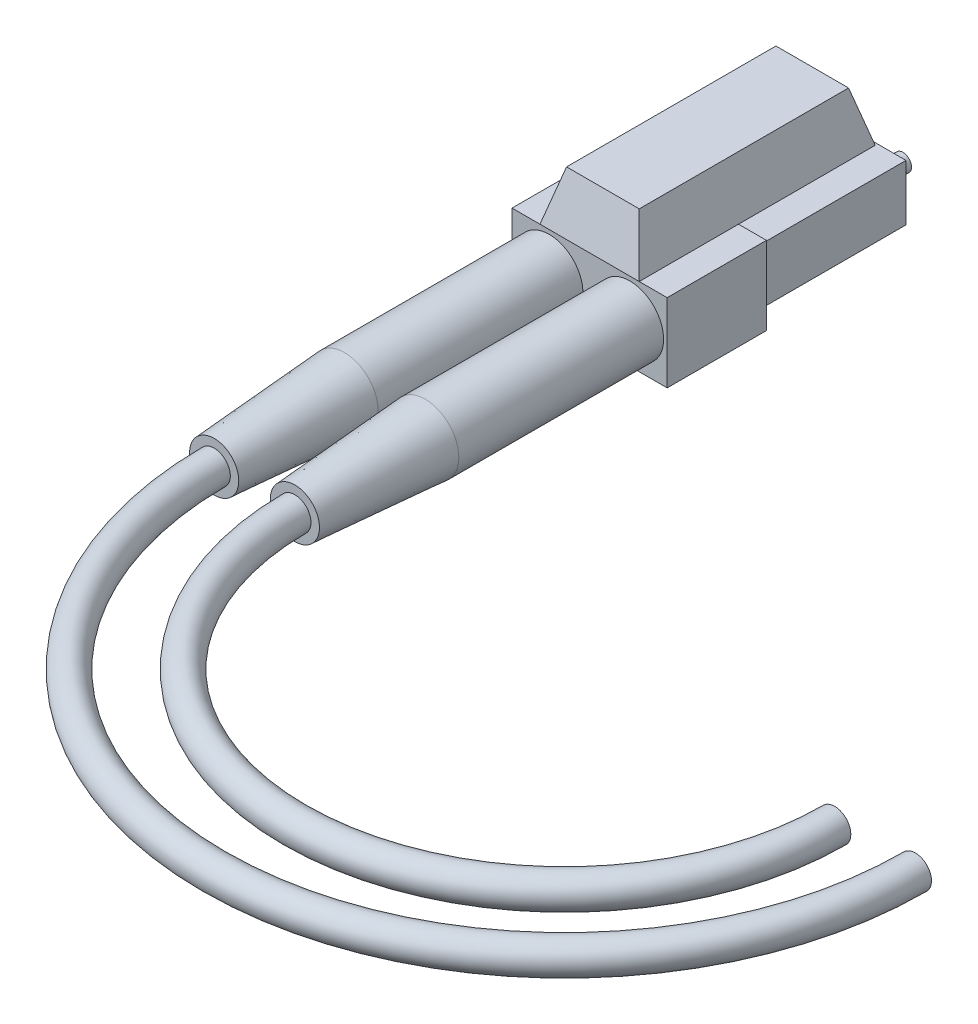
SolidWorks part; units mm, degrees
ref_plane "Front" through (0, 0, 0) normal (0, 0, 1) x (1, 0, 0)
ref_plane "Top" through (0, 0, 0) normal (0, 1, 0) x (1, 0, 0)
ref_plane "Right" through (0, 0, 0) normal (1, 0, 0) x (0, 0, -1)
sketch "Sketch1" plane through (0, 0, 0) normal (0, 0, 1) x (1, 0, 0)
  line L0 (0.9959, 4.5) -> (5.4959, 4.5)
  line L1 (-5.5041, 4.5) -> (-1.0041, 4.5)
  line L2 (-5.5041, 4.5) -> (-5.5041, 0)
  line L3 (-5.5041, 0) -> (-1.0041, 0)
  line L4 (-1.0041, 4.5) -> (-1.0041, 0)
  line L5 (0.9959, 4.5) -> (0.9959, 0)
  line L6 (0.9959, 0) -> (5.4959, 0)
  line L7 (5.4959, 4.5) -> (5.4959, 0)
  dimension "D1" = 2
extrude "Boss-Extrude1" add sketch "Sketch1" against normal blind 12
sketch "Sketch2" plane through (0, 0, -12) normal (0, 0, -1) x (-1, 0, 0)
  circle A0 centre (3.25, 2.25) radius 0.6917
  circle A1 centre (-3.25, 2.25) radius 0.6917
  dimension "D1" = 2
extrude "Boss-Extrude2" add sketch "Sketch2" along normal blind 2
sketch "Sketch3" plane through (0, 0, 0) normal (0, 0, 1) x (1, 0, 0)
  line L1 (-6.25, -1) -> (6.25, -1)
  line L2 (-6.25, -1) -> (-6.25, 5.3)
  line L3 (-6.25, 5.3) -> (6.25, 5.3)
  line L4 (6.25, -1) -> (6.25, 5.3)
extrude "Boss-Extrude3" add sketch "Sketch3" along normal blind 8 contours L1 L4 L3 L2
sketch "Sketch4" plane through (0, 0, 8) normal (0, 0, 1) x (1, 0, 0)
  circle A0 centre (3.25, 2.25) radius 2.715
  circle A1 centre (-3.25, 2.25) radius 2.715
extrude "Boss-Extrude4" add sketch "Sketch4" along normal blind 16.5
sketch "Sketch5" plane through (0, 0, 24.5) normal (0, 0, 1) x (1, 0, 0)
  circle A0 centre (-3.25, 2.25) radius 2.715
  circle A1 centre (3.25, 2.25) radius 2.715
extrude "Boss-Extrude5" add sketch "Sketch5" along normal blind 10.5 draft 4
sketch "Sketch6" plane through (0, 0, 35) normal (0, 0, 1) x (1, 0, 0)
  circle A0 centre (3.25, 2.25) radius 1.375
  circle A1 centre (-3.25, 2.25) radius 1.375
extrude "Boss-Extrude6" [suppressed] add sketch "Sketch6" along normal blind 23
sketch "Sketch7" [suppressed] plane through (0, 0, 58) normal (0, 0, 1) x (1, 0, 0)
  circle A0 centre (3.25, 2.25) radius 1
  circle A1 centre (-3.25, 2.25) radius 1
extrude "Boss-Extrude7" [suppressed] add sketch "Sketch7" along normal blind 25
sketch "Sketch8" plane through (0, 5.3, 0) normal (0, 1, 0) x (1, 0, 0)
  line L0 (-6.25, -8) -> (6.25, -8) construction
  line L1 (4, -8) -> (-4, -8)
  line L2 (4, -8) -> (4, 11.0144)
  line L3 (4, 11.0144) -> (-4, 11.0144)
  line L4 (-4, -8) -> (-4, 11.0144)
extrude "Boss-Extrude8" add sketch "Sketch8" along normal blind 4 draft 15
sketch "profile1" plane through (0, 0, 35) normal (0, 0, 1) x (1, 0, 0)
  circle A0 centre (-3.25, 2.25) radius 1.3
  circle A1 centre (3.25, 2.25) radius 1.3
ref_plane "Plane1" through (0, 2.25, 0) normal (0, -1, 0) x (1, 0, 0)
sketch "path1" plane through (0, 2.25, 0) normal (0, -1, 0) x (1, 0, 0)
  line L0 (-1.2692, 35) -> (1.2692, 35) construction
  line L1 (0, 35) -> (50, 35) construction
  arc A0 (0, 35) -> (50, 35) centre (25, 35) cw
sweep "Sweep1" add profiles "profile1" path "path1"
sketch "pathA" [suppressed] plane through (0, 2.25, 2.25) normal (0, 1, 0) x (1, 0, 0)
  line L0 (-1.2692, -32.75) -> (1.2692, -32.75) construction
  line L1 (0, -32.75) -> (-50, -32.75) construction
  arc A0 (0, -32.75) -> (-50, -32.75) centre (-25, -32.75) cw
sketch "profileA" [suppressed] plane through (0, 0, 35) normal (0, 0, 1) x (1, 0, 0)
  circle A0 centre (-3.25, 2.25) radius 1.3
  circle A1 centre (3.25, 2.25) radius 1.3
sweep "Sweep2" [suppressed] add profiles "profileA" path "pathA"
